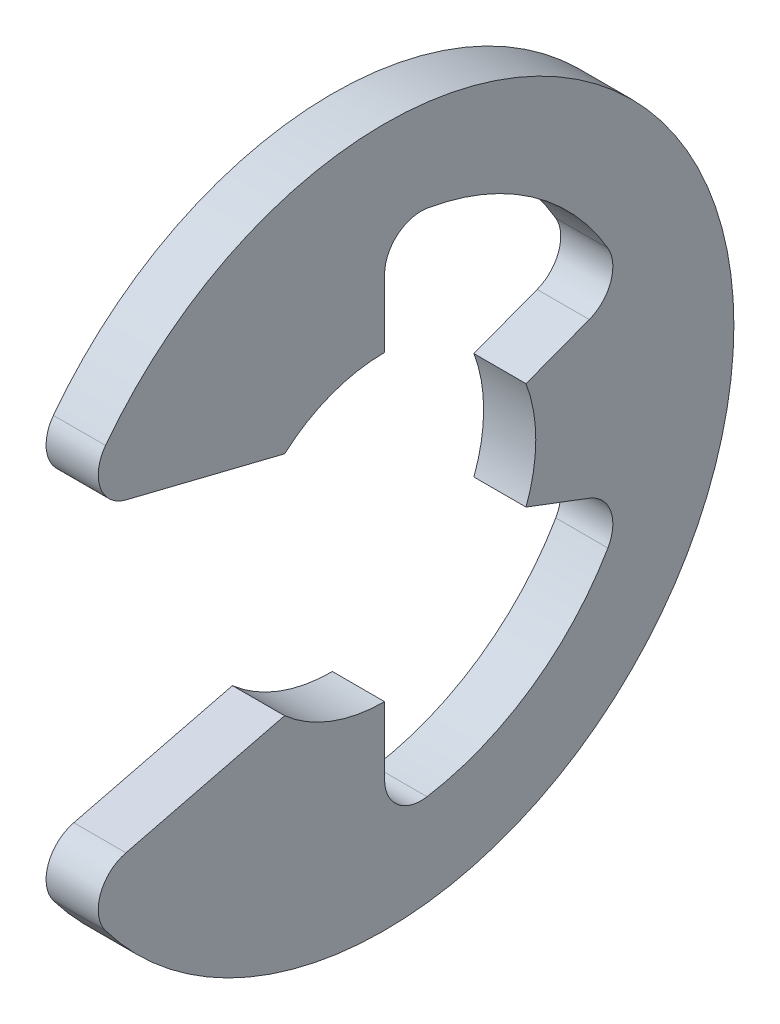
SolidWorks part; units mm, degrees
material "AISI 1020"
ref_plane "Front" through (0, 0, 0) normal (0, 0, 1) x (1, 0, 0)
ref_plane "Top" through (0, 0, 0) normal (0, 1, 0) x (1, 0, 0)
ref_plane "Right" through (0, 0, 0) normal (1, 0, 0) x (0, 0, -1)
sketch "Sketch1" plane through (0, 0, 0) normal (1, 0, 0) x (0, 0, -1)
  line L0 (-3.7499, -2.0097) -> (-1.218, -1.3811)
  line L1 (-3.7499, 2.0097) -> (-1.218, 1.3811)
  line L2 (0, -1.8415) -> (0, -3.1463)
  line L3 (0, 1.8415) -> (0, 3.1463)
  line L4 (1.7226, -0.6511) -> (2.9431, -1.1124)
  line L5 (1.7226, 0.6511) -> (2.9431, 1.1124)
  line L6 (0, 0) -> (-4.445, 0) construction
  line L7 (1.7226, 0.6511) -> (1.7226, -0.6511) construction
  line L8 (0, -1.8415) -> (-1.218, -1.3811) construction
  line L9 (0, 4.2545) -> (0, -4.2545) construction
  circle A1 centre (0, 0) radius 4.445 construction
  circle A2 centre (0, 0) radius 1.8415 construction
  arc A3 (-3.7499, -2.0097) -> (-3.7499, 2.0097) centre (0, 0) ccw
  arc A4 (-1.218, -1.3811) -> (0, -1.8415) centre (0, 0) ccw
  arc A5 (-1.218, 1.3811) -> (0, 1.8415) centre (0, 0) cw
  arc A6 (1.7226, 0.6511) -> (1.7226, -0.6511) centre (0, 0) cw
  arc A7 (0, -3.1463) -> (2.9431, -1.1124) centre (0, 0) ccw
  arc A8 (2.9431, 1.1124) -> (0, 3.1463) centre (0, 0) ccw
  dimension "D1" = 3.1463
  dimension "OD" = 8.509
  dimension "L" = 8.89
  dimension "D" = 3.683
  dimension "D2" = 2.0939
  dimension "D3" = 2.7622
extrude "Extrude1" add sketch "Sketch1" along normal mid plane 0.635
fillet "Fillet1" radius 0.4445 6 edges at (0, -3.1463, 0) (0, 3.1463, 0) (0, -2.0097, 3.7499) (0, 2.0097, 3.7499) (0, -1.1124, -2.9431) (0, 1.1124, -2.9431)
sketch "Sketch3" plane through (0, 0, 0) normal (0, 1, 0) x (1, 0, 0)
  line L0 (0.3683, 2.3876) -> (0.3683, 1.8669)
  line L1 (0.3683, 1.8669) -> (-0.3683, 1.8669)
  line L2 (-0.3683, 1.8669) -> (-0.3683, 2.3876)
  line L3 (-0.3683, 2.3876) -> (-5.1562, 2.3876)
  line L4 (2.2098, 0) -> (2.2098, 2.1272)
  line L5 (-5.1562, 2.3876) -> (-5.1562, 0)
  line L6 (-5.1562, 0) -> (2.2098, 0)
  line L8 (2.2098, 0) -> (2.2098, 2.3876) construction
  line L9 (2.2098, 2.3876) -> (0.3683, 2.3876) construction
  line L10 (2.2098, 0) -> (17.2631, 0) construction
  line L11 (2.2098, 2.1272) -> (1.9494, 2.3876)
  line L12 (1.9494, 2.3876) -> (0.3683, 2.3876)
  point P2 (0, 1.8669)
  point P5 (0.3683, 2.1272)
  dimension "D1" = 1.8415
  dimension "Ds" = 4.7752
  dimension "Dg" = 3.7338
  dimension "W" = 0.7366
  dimension "D2" = 7.366
  dimension "D3" = 45
revolve "Revolve2" [suppressed] add sketch "Sketch3" angle 360 about L10
equation "\"D2@Sketch3\" = \"W@Sketch3\"*10"
equation "\"D1@Sketch3\" = \"D2@Sketch3\"/4"
equation "\"D1@Sketch1\" = (\"OD@Sketch1\"+\"D@Sketch1\")/3.875"
equation "\"D3@Sketch1\" = \"D@Sketch1\"*.75"
equation "\"D1@Fillet1\" = \"D1@Extrude1\"*.7"
